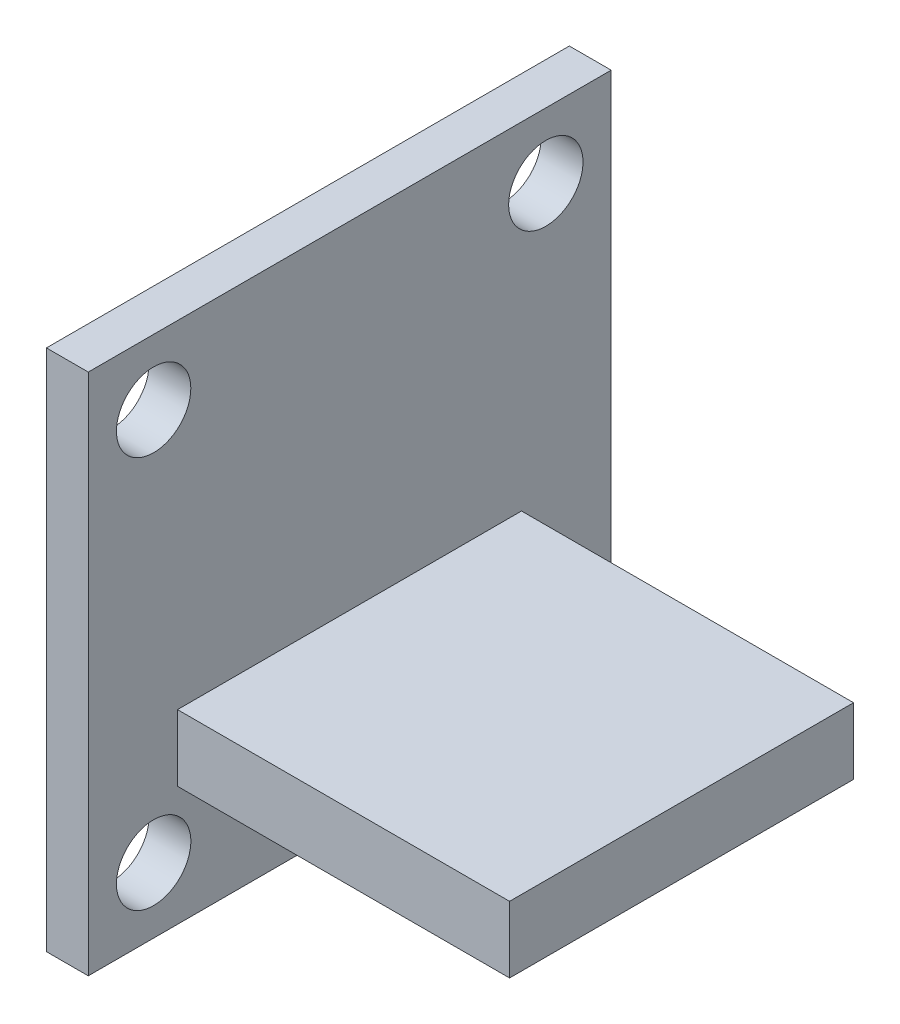
SolidWorks part; units mm, degrees
ref_plane "Front Plane" through (0, 0, 0) normal (0, 0, 1) x (1, 0, 0)
ref_plane "Top Plane" through (0, 0, 0) normal (0, 1, 0) x (1, 0, 0)
ref_plane "Right Plane" through (0, 0, 0) normal (1, 0, 0) x (0, 0, -1)
sketch "Sketch1" plane through (0, 0, 0) normal (1, 0, 0) x (0, 0, -1)
  line L1 (0, 0) -> (20, 0)
  line L2 (0, 0) -> (0, 20)
  line L3 (0, 20) -> (20, 20)
  line L4 (20, 0) -> (20, 20)
  dimension "D1" = 20
  dimension "D2" = 20
extrude "Extrude1" add sketch "Sketch1" along normal blind 1.6002
sketch "Sketch2" plane through (1.6002, 0, 0) normal (1, 0, 0) x (0, 0, -1)
  line L0 (10, 20) -> (10, 0) construction
  line L1 (20, 20) -> (0, 20) construction
  line L2 (0, 0) -> (20, 0) construction
  line L3 (0, 10) -> (20, 10) construction
  line L4 (0, 20) -> (0, 0) construction
  line L5 (20, 0) -> (20, 20) construction
  circle A0 centre (2.5, 17.5) radius 1.4224
  circle A1 centre (17.5, 17.5) radius 1.4224
  circle A2 centre (17.5, 2.5) radius 1.4224
  circle A3 centre (2.5, 2.5) radius 1.4224
  dimension "D1" = 2.8448
  dimension "D2" = 7.5
  dimension "D3" = 7.5
extrude "Cut-Extrude1" cut sketch "Sketch2" against normal through all
sketch "Sketch3" plane through (1.6002, 0, 0) normal (1, 0, 0) x (0, 0, -1)
  line L0 (0, 0) -> (20, 0) construction
  line L1 (3.4138, 7.112) -> (16.571, 7.112)
  line L2 (3.4138, 7.112) -> (3.4138, 4.572)
  line L3 (3.4138, 4.572) -> (16.571, 4.572)
  line L4 (16.571, 7.112) -> (16.571, 4.572)
  line L5 (20, 0) -> (20, 20) construction
  dimension "D1" = 13.1572
  dimension "D2" = 2.54
  dimension "D3" = 4.572
  dimension "D4" = 3.429
extrude "Extrude2" add sketch "Sketch3" along normal blind 12.7
